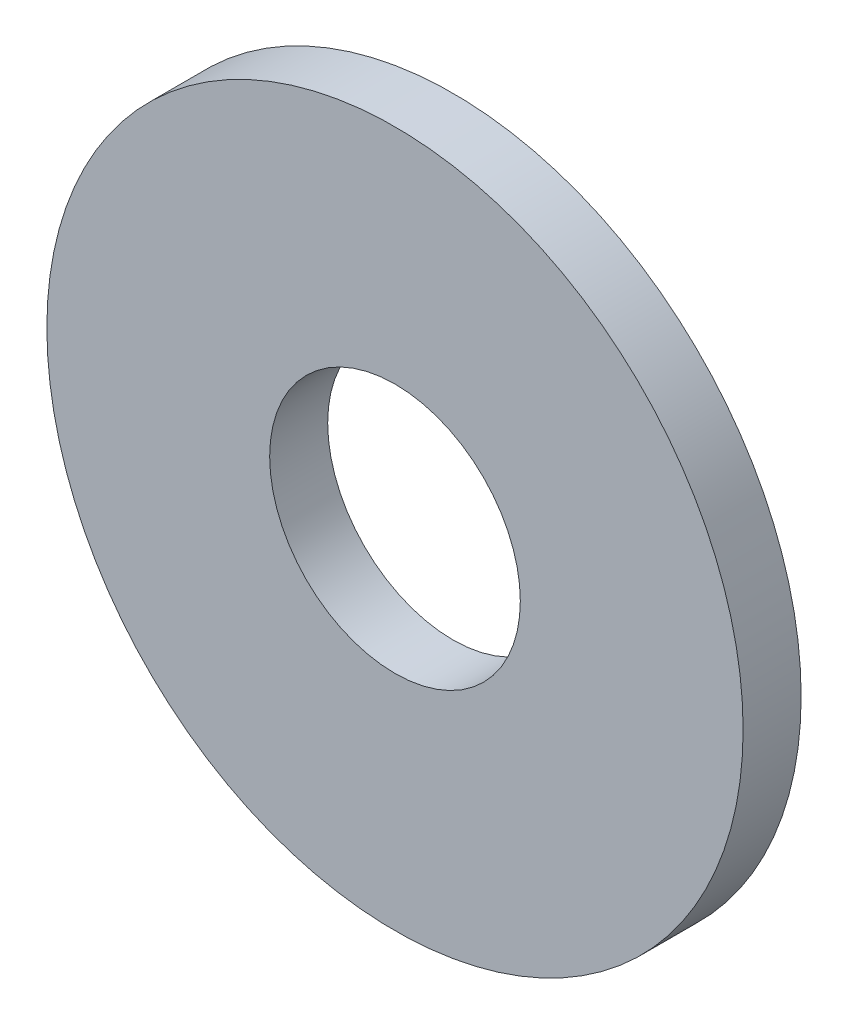
SolidWorks part; units mm, degrees
ref_plane "Front Plane" through (0, 0, 0) normal (0, 0, 1) x (1, 0, 0)
ref_plane "Top Plane" through (0, 0, 0) normal (0, 1, 0) x (1, 0, 0)
ref_plane "Right Plane" through (0, 0, 0) normal (1, 0, 0) x (0, 0, -1)
sketch "Sketch1" plane through (0, 0, 0) normal (0, 0, 1) x (1, 0, 0)
  circle A0 centre (0, 0) radius 9.525
  circle A1 centre (0, 0) radius 3.429
  dimension "D1" = 19.05
  dimension "D2" = 6.858
extrude "Boss-Extrude1" add sketch "Sketch1" along normal blind 1.5875
